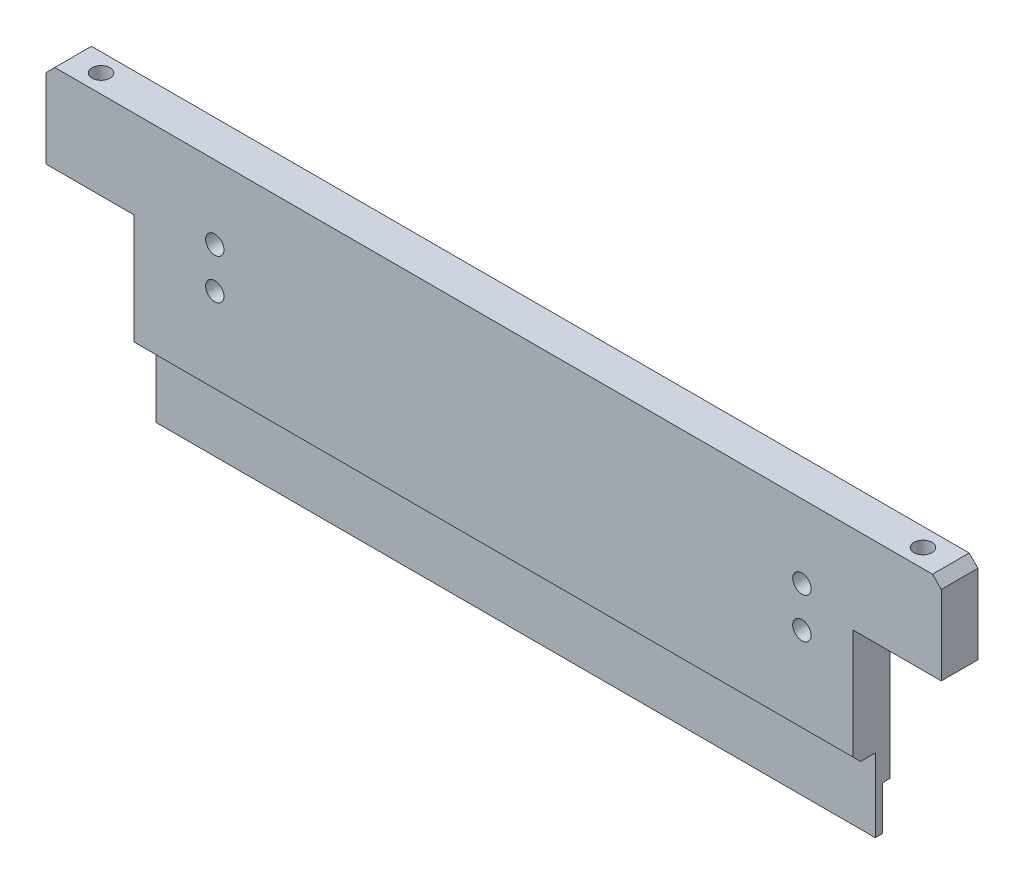
SolidWorks part; units mm, degrees
ref_plane "Front Plane" through (0, 0, 0) normal (0, 0, 1) x (1, 0, 0)
ref_plane "Top Plane" through (0, 0, 0) normal (0, 1, 0) x (1, 0, 0)
ref_plane "Right Plane" through (0, 0, 0) normal (1, 0, 0) x (0, 0, -1)
sketch "Sketch1" plane through (0, 0, 0) normal (0, 0, 1) x (1, 0, 0)
  line L0 (-61, 17.8) -> (-59.8, 19)
  line L1 (-59.8, 19) -> (59.8, 19)
  line L2 (-61, 17.8) -> (-61, -19)
  line L3 (-61, -19) -> (61, -19)
  line L4 (61, 17.8) -> (61, -19)
  line L5 (-61, 19) -> (61, -19) construction
  line L6 (-61, -19) -> (61, 19) construction
  line L7 (59.8, 19) -> (61, 17.8)
  point P0 (0, 0)
  dimension "D1" = 122
  dimension "D2" = 38
extrude "Boss-Extrude1" add sketch "Sketch1" along normal blind 5
sketch "Sketch2" plane through (0, 0, 5) normal (0, 0, 1) x (1, 0, 0)
  line L1 (49, 7) -> (61, 7)
  line L2 (49, 7) -> (49, -19)
  line L3 (49, -19) -> (61, -19)
  line L4 (61, 7) -> (61, -19)
  dimension "D1" = 12
  dimension "D2" = 26
extrude "Cut-Extrude1" cut sketch "Sketch2" against normal through all
sketch "Sketch3" plane through (0, 0, 5) normal (0, 0, 1) x (1, 0, 0)
  line L0 (49, 7) -> (49, -19) construction
  line L1 (59.8, 19) -> (-59.8, 19) construction
  circle A0 centre (42, 9) radius 1.25
  circle A1 centre (42, 3.5) radius 1.25
  circle A2 centre (-38, 9) radius 1.25
  circle A3 centre (-38, 3.5) radius 1.25
  point P12 (0, 0)
  dimension "D1" = 5.5
  dimension "D2" = 2.5
  dimension "D3" = 7
  dimension "D4" = 10
  dimension "D5" = 80
  dimension "D6" = 5.5
extrude "Cut-Extrude2" cut sketch "Sketch3" against normal through all
sketch "Sketch4" plane through (0, 7, 0) normal (0, -1, 0) x (1, 0, 0)
  line L0 (61, 0) -> (61, 5) construction
  circle A0 centre (56, 2.5) radius 1.23
  point P5 (61, 2.5)
  dimension "D1" = 2.46
  dimension "D2" = 5
extrude "Cut-Extrude3" cut sketch "Sketch4" against normal through all
mirror "Mirror1" about plane through (0, 0, 0) normal (1, 0, 0) of "Cut-Extrude3", "Cut-Extrude1"
sketch "Sketch5" plane through (0, 0, 5) normal (0, 0, 1) x (1, 0, 0)
  line L1 (-49, -9) -> (49, -9)
  line L2 (-49, -9) -> (-49, -19)
  line L3 (-49, -19) -> (49, -19)
  line L4 (49, -9) -> (49, -19)
  line L5 (-49, 7) -> (-49, -19) construction
  dimension "D1" = 10
extrude "Cut-Extrude4" cut sketch "Sketch5" against normal blind 3
sketch "Sketch6" plane through (0, 0, 0) normal (0, 0, -1) x (-1, 0, 0)
  line L0 (-49, 7) -> (-49, -19) construction
  line L1 (-49, -13) -> (49, -13)
  line L2 (-49, -13) -> (-49, -19)
  line L3 (-49, -19) -> (49, -19)
  line L4 (49, -13) -> (49, -19)
  dimension "D1" = 6
extrude "Cut-Extrude5" cut sketch "Sketch6" against normal blind 1
chamfer "Chamfer1" distance 1 angle 45 1 edges at (0, -9, 5)
